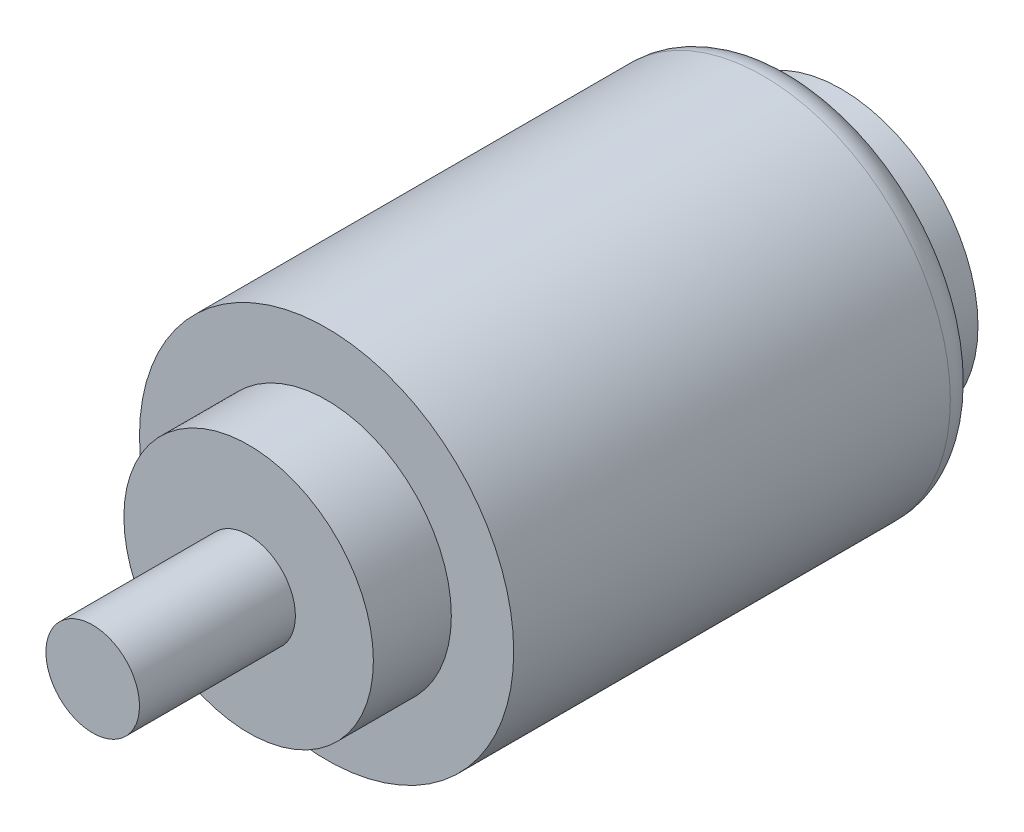
SolidWorks part; units mm, degrees
ref_plane "Front Plane" through (0, 0, 0) normal (0, 0, 1) x (1, 0, 0)
ref_plane "Top Plane" through (0, 0, 0) normal (0, 1, 0) x (1, 0, 0)
ref_plane "Right Plane" through (0, 0, 0) normal (1, 0, 0) x (0, 0, -1)
sketch "Sketch1" plane through (0, 0, 0) normal (0, 0, 1) x (1, 0, 0)
  circle A0 centre (5.1787, -6.9251) radius 12
extrude "Boss-Extrude1" add sketch "Sketch1" along normal blind 30
sketch "Sketch2" plane through (0, 0, 30) normal (0, 0, 1) x (1, 0, 0)
  circle A0 centre (5.1787, -6.9251) radius 8
extrude "Boss-Extrude2" add sketch "Sketch2" along normal blind 5
sketch "Sketch4" plane through (0, 0, 35) normal (0, 0, 1) x (1, 0, 0)
  circle A1 centre (5.1787, 2.9956) radius 1.5793
  circle A2 centre (15.0994, -6.9251) radius 1.5793
  circle A3 centre (5.1787, -16.8458) radius 1.5793
  circle A4 centre (-4.742, -6.9251) radius 1.5793
  point P14 (5.1787, -6.9251)
  dimension "D1" = 4
extrude "Cut-Extrude3" cut sketch "Sketch4" against normal blind 3
sketch "Sketch5" plane through (0, 0, 35) normal (0, 0, 1) x (1, 0, 0)
  circle A0 centre (5.1787, -6.9251) radius 3
extrude "Boss-Extrude3" add sketch "Sketch5" along normal blind 10
sketch "Sketch6" plane through (0, 0, 0) normal (0, 0, -1) x (-1, 0, 0)
  circle A0 centre (-5.1787, -6.9251) radius 8.774
extrude "Boss-Extrude4" add sketch "Sketch6" along normal blind 3
fillet "Fillet1" radius 2 1 edges at (17.1787, -6.9251, 0)
